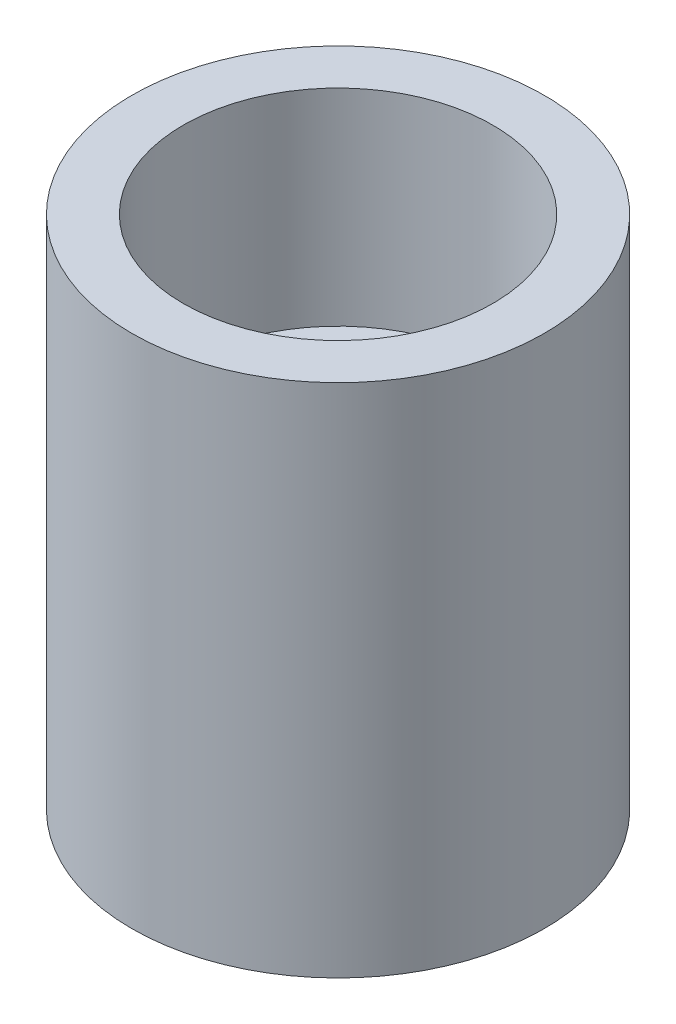
SolidWorks part; units mm, degrees
ref_plane "Front Plane" through (0, 0, 0) normal (0, 0, 1) x (1, 0, 0)
ref_plane "Top Plane" through (0, 0, 0) normal (0, 1, 0) x (1, 0, 0)
ref_plane "Right Plane" through (0, 0, 0) normal (1, 0, 0) x (0, 0, -1)
sketch "Sketch1" plane through (0, 0, 0) normal (0, 1, 0) x (1, 0, 0)
  circle A0 centre (0, 0) radius 2
  dimension "D1" = 4
extrude "Boss-Extrude1" add sketch "Sketch1" along normal blind 5
sketch "Sketch2" plane through (0, 5, 0) normal (0, 1, 0) x (1, 0, 0)
  circle A0 centre (0, 0) radius 1.5
  dimension "D1" = 3
extrude "Cut-Extrude1" cut sketch "Sketch2" against normal blind 2
ref_point "Point1"
